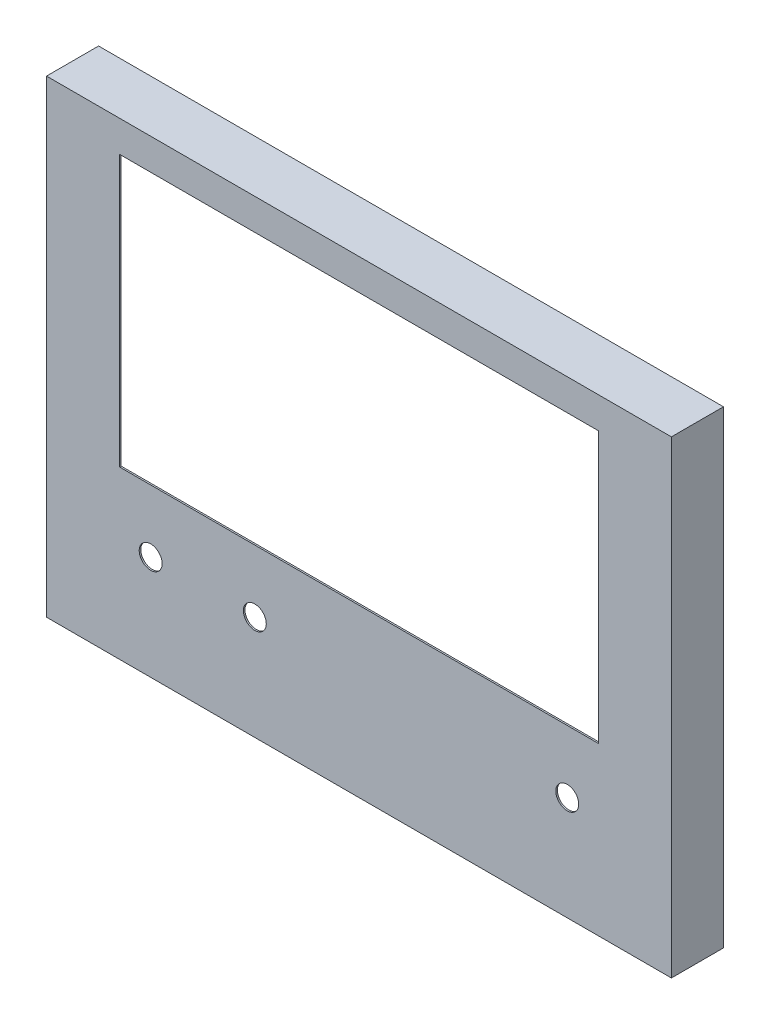
SolidWorks part; units mm, degrees
ref_plane "Front Plane" through (0, 0, 0) normal (0, 0, 1) x (1, 0, 0)
ref_plane "Top Plane" through (0, 0, 0) normal (0, 1, 0) x (1, 0, 0)
ref_plane "Right Plane" through (0, 0, 0) normal (1, 0, 0) x (0, 0, -1)
sketch "Sketch1" plane through (0, 0, 0) normal (0, 0, 1) x (1, 0, 0)
  line L1 (300, 225) -> (-300, 225)
  line L2 (300, 225) -> (300, -225)
  line L3 (300, -225) -> (-300, -225)
  line L4 (-300, 225) -> (-300, -225)
  line L5 (300, 225) -> (-300, -225) construction
  line L6 (300, -225) -> (-300, 225) construction
  point P0 (0, 0)
  dimension "D1" = 600
  dimension "D2" = 450
extrude "Boss-Extrude1" add sketch "Sketch1" along normal blind 50
shell "Shell1" thickness 1.5
sketch "Sketch3" plane through (0, 0, 50) normal (0, 0, 1) x (1, 0, 0)
  line L0 (300, 225) -> (-300, 225) construction
  line L1 (-230, 195) -> (230, 195)
  line L2 (-230, 195) -> (-230, -65)
  line L3 (-230, -65) -> (230, -65)
  line L4 (230, 195) -> (230, -65)
  line L5 (-300, 225) -> (-300, -225) construction
  dimension "D1" = 460
  dimension "D2" = 260
  dimension "D3" = 30
  dimension "D4" = 70
extrude "Cut-Extrude1" cut sketch "Sketch3" against normal up to next
sketch "Sketch4" plane through (0, 0, 50) normal (0, 0, 1) x (1, 0, 0)
  line L0 (-300, -125) -> (300, -125) construction
  line L1 (-300, 225) -> (-300, -225) construction
  line L2 (300, -225) -> (300, 225) construction
  line L3 (-300, -225) -> (300, -225) construction
  circle A0 centre (-200, -125) radius 11
  circle A1 centre (200, -125) radius 11
  circle A2 centre (-100, -125) radius 11
  dimension "D1" = 22
  dimension "D2" = 22
  dimension "D3" = 22
  dimension "D5" = 100
  dimension "D6" = 100
  dimension "D4" = 100
  dimension "D7" = 100
extrude "Cut-Extrude2" cut sketch "Sketch4" against normal up to next
